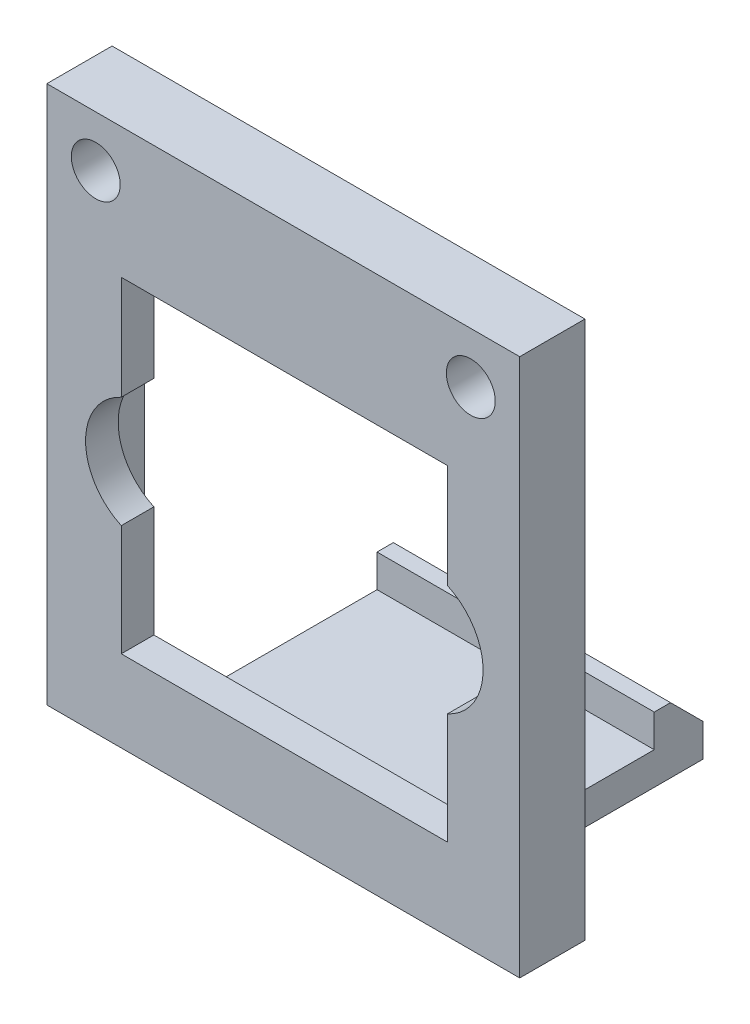
SolidWorks part; units mm, degrees
material "ABS"
ref_plane "Front Plane" through (0, 0, 0) normal (0, 0, 1) x (1, 0, 0)
ref_plane "Top Plane" through (0, 0, 0) normal (0, 1, 0) x (1, 0, 0)
ref_plane "Right Plane" through (0, 0, 0) normal (1, 0, 0) x (0, 0, -1)
sketch "Sketch1" plane through (0, 0, 0) normal (0, 0, 1) x (1, 0, 0)
  line L1 (0, 0) -> (29, 0)
  line L2 (0, 0) -> (0, 55.5)
  line L3 (0, 55.5) -> (29, 55.5)
  line L4 (29, 0) -> (29, 55.5)
  dimension "D1" = 55.5
  dimension "D2" = 29
extrude "Body" add sketch "Sketch1" along normal blind 4
sketch "Sketch2" plane through (0, 0, 4) normal (0, 0, 1) x (1, 0, 0)
  line L0 (14.5, 55.5) -> (14.5, 0) construction
  line L1 (29, 55.5) -> (0, 55.5) construction
  line L2 (0, 0) -> (29, 0) construction
  line L3 (0, 27.75) -> (29, 27.75) construction
  line L4 (0, 55.5) -> (0, 0) construction
  line L5 (29, 0) -> (29, 55.5) construction
  circle A0 centre (3, 52.385) radius 1.5
  circle A1 centre (26, 52.385) radius 1.5
  circle A2 centre (26, 3.115) radius 1.5
  circle A3 centre (3, 3.115) radius 1.5
  dimension "D1" = 3
  dimension "D2" = 11.5
  dimension "D3" = 24.635
extrude "Bolt Holes" cut sketch "Sketch2" against normal through all
sketch "Sketch4" plane through (0, 0, 0) normal (0, 0, 1) x (1, 0, 0)
  line L0 (14.5639, 77.2184) -> (14.5639, 21.7184) construction
  line L3 (0.0639, 49.4684) -> (29.0639, 49.4684) construction
  line L6 (29, 37.7184) -> (0, 37.7184) construction
  line L7 (4.5639, 34.3083) -> (4.5639, 27.5)
  line L8 (24.5639, 34.3083) -> (24.5639, 27.5)
  line L9 (29, 0) -> (29, 55.5) construction
  line L10 (0, 55.5) -> (0, 0) construction
  line L11 (29, 55.5) -> (0, 55.5) construction
  line L12 (4.5639, 47.5) -> (24.5639, 47.5)
  line L13 (4.5639, 47.5) -> (4.5639, 41.1285)
  line L14 (4.5639, 27.5) -> (24.5639, 27.5)
  line L15 (24.5639, 47.5) -> (24.5639, 41.1285)
  circle A1 centre (6.1239, 37.7184) radius 3.75 construction
  circle A2 centre (23.0039, 37.7184) radius 3.75 construction
  arc A3 (4.5639, 41.1285) -> (4.5639, 34.3083) centre (6.1239, 37.7184) ccw
  arc A4 (24.5639, 41.1285) -> (24.5639, 34.3083) centre (23.0039, 37.7184) cw
  dimension "D3" = 7.5
  dimension "D5" = 8.44
  dimension "D8" = 20
  dimension "D7" = 20
  dimension "8.62mm" = 8
extrude "Cut-Extrude1" cut sketch "Sketch4" along normal blind 10
sketch "Sketch6" plane through (0, 0, 0) normal (0, 0, -1) x (-1, 0, 0)
  line L0 (-29, 55.5) -> (0, 55.5) construction
  line L3 (-29, 0) -> (-29, 55.5) construction
  line L6 (-14.5, 3.573) -> (-14.5, 59.073) construction
  line L13 (-27, 49.5) -> (-2, 49.5)
  line L14 (-27, 49.5) -> (-27, 24.5)
  line L15 (-27, 24.5) -> (-2, 24.5)
  line L16 (-2, 49.5) -> (-2, 24.5)
  line L17 (-60.8742, 6.688) -> (-37.8742, 6.688) construction
  point P4 (-19.9715, 54.5517)
  dimension "D1" = 6
  dimension "D2" = 25
  dimension "D3" = 2
extrude "Cut-Extrude2" cut sketch "Sketch6" against normal blind 2
sketch "Sketch7" plane through (0, 0, 0) normal (0, 0, 1) x (1, 0, 0)
  line L1 (6, 24.5) -> (23, 24.5)
  line L2 (6, 24.5) -> (6, 22.5)
  line L3 (6, 22.5) -> (23, 22.5)
  line L4 (23, 24.5) -> (23, 22.5)
  line L5 (14.5, 0) -> (14.5, 55.5) construction
  line L8 (3, 3.115) -> (3, 6.115) construction
  line L9 (3, 3.115) -> (6, 3.115) construction
  line L10 (6, 3.115) -> (6, 22.5) construction
  line L11 (27, 24.5) -> (2, 24.5) construction
  point P8 (14.5, 24.5)
  point P11 (14.5, 24.5)
  dimension "D1" = 2
extrude "Boss-Extrude1" add sketch "Sketch7" against normal blind 10.25
sketch "Sketch8" plane through (23, 0, 0) normal (1, 0, 0) x (0, 0, -1)
  line L0 (10.25, 22.5) -> (10.25, 26.5)
  line L1 (10.25, 26.5) -> (11.25, 26.5)
  line L2 (11.25, 26.5) -> (13.25, 24.5)
  line L3 (13.25, 24.5) -> (13.25, 22.5)
  line L4 (13.25, 22.5) -> (10.25, 22.5)
  dimension "D1" = 4
  dimension "D2" = 1
  dimension "D3" = 2
  dimension "D4" = 3
extrude "Boss-Extrude2" add sketch "Sketch8" against normal up to surface (17 mm away) up to face at (6, 23.75, -6.4063)
ref_plane "Plane1" through (0, 22.5, 0) normal (0, -1, 0) x (-1, 0, 0)
other "SurfaceCut1"
